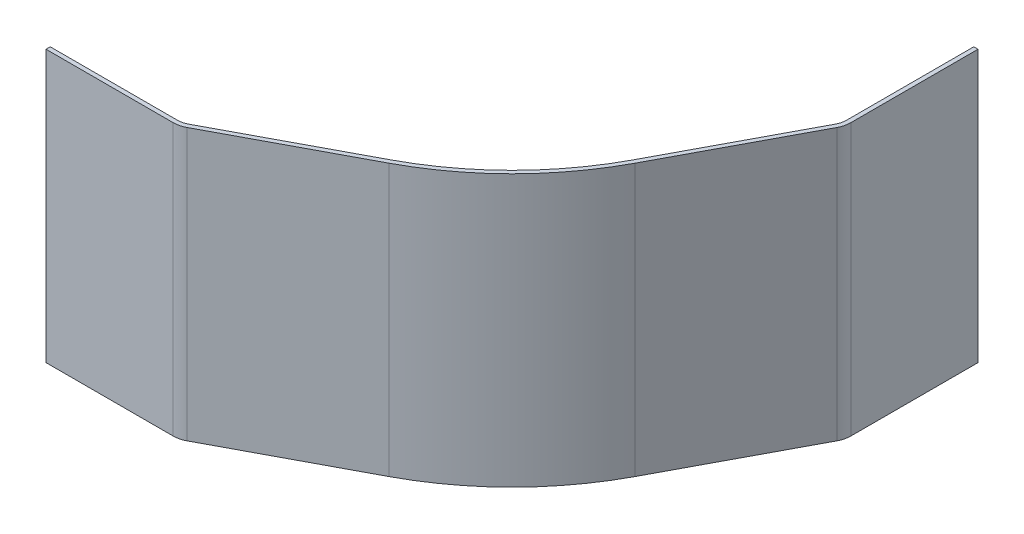
SolidWorks part; units mm, degrees
ref_plane "Front Plane" through (0, 0, 0) normal (0, 0, 1) x (1, 0, 0)
ref_plane "Top Plane" through (0, 0, 0) normal (0, 1, 0) x (1, 0, 0)
ref_plane "Right Plane" through (0, 0, 0) normal (1, 0, 0) x (0, 0, -1)
sketch "Sketch1" plane through (0, 0, 0) normal (0, -1, 0) x (0, 0, -1)
  line L0 (0, 17) -> (0.22, 17) construction
  line L1 (0.22, 17) -> (0.22, 19.5) construction
  line L2 (0.22, 19.5) -> (7.72, 19.5) construction
  line L3 (-17, 0) -> (-17, -0.22) construction
  line L4 (-17, -0.22) -> (-19.5, -0.22) construction
  line L5 (-19.5, -0.22) -> (-19.5, -7.72) construction
  line L6 (-15.2346, 8.0913) -> (-19.3686, 0.3077)
  line L7 (-8.0913, 15.2346) -> (-0.3077, 19.3686)
  line L8 (-19.5, -0.22) -> (-19.5, -7.72)
  line L9 (0.22, 19.5) -> (7.72, 19.5)
  line L10 (0.22, 19.75) -> (7.72, 19.75)
  line L11 (-8.2085, 15.4554) -> (-0.425, 19.5894)
  line L12 (-15.4554, 8.2085) -> (-19.5894, 0.425)
  line L13 (-19.75, -0.22) -> (-19.75, -7.72)
  line L14 (-19.5, -7.72) -> (-19.75, -7.72)
  line L15 (7.72, 19.5) -> (7.72, 19.75)
  circle A0 centre (0, 0) radius 17 construction
  arc A1 (-15.2346, 8.0913) -> (-8.0913, 15.2346) centre (0, 0) cw
  arc A2 (-0.3077, 19.3686) -> (0.22, 19.5) centre (0.22, 18.375) cw
  arc A3 (-19.3686, 0.3077) -> (-19.5, -0.22) centre (-18.375, -0.22) ccw
  arc A4 (-0.425, 19.5894) -> (0.22, 19.75) centre (0.22, 18.375) cw
  arc A5 (-15.4554, 8.2085) -> (-8.2085, 15.4554) centre (0, 0) cw
  arc A6 (-19.5894, 0.425) -> (-19.75, -0.22) centre (-18.375, -0.22) ccw
  dimension "D1" = 34
  dimension "D8" = 17.25
  dimension "D10" = 18.375
  dimension "D2" = 17.22
  dimension "D3" = 17.22
  dimension "D4" = 2.5
  dimension "D5" = 2.5
  dimension "D6" = 7.5
  dimension "D7" = 7.5
  dimension "D9" = 0.25
  dimension "D11" = 18.375
extrude "Extrude1" add sketch "Sketch1" along normal mid plane 16
